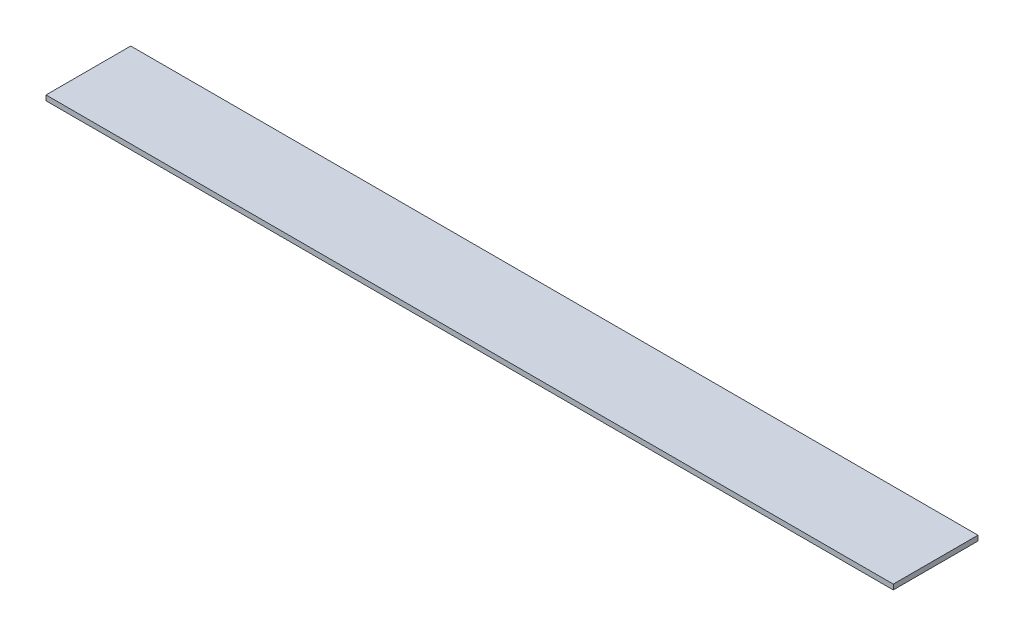
SolidWorks part; units mm, degrees
ref_plane "Front Plane" through (0, 0, 0) normal (0, 0, 1) x (1, 0, 0)
ref_plane "Top Plane" through (0, 0, 0) normal (0, 1, 0) x (1, 0, 0)
ref_plane "Right Plane" through (0, 0, 0) normal (1, 0, 0) x (0, 0, -1)
sketch "Sketch1" plane through (0, 0, 0) normal (0, 1, 0) x (1, 0, 0)
  line L0 (250, -25) -> (-250, -25)
  line L1 (-250, -25) -> (-250, 25)
  line L2 (-250, 25) -> (250, 25)
  line L3 (250, 25) -> (250, -25)
extrude "Boss-Extrude1" add sketch "Sketch1" along normal blind 3
